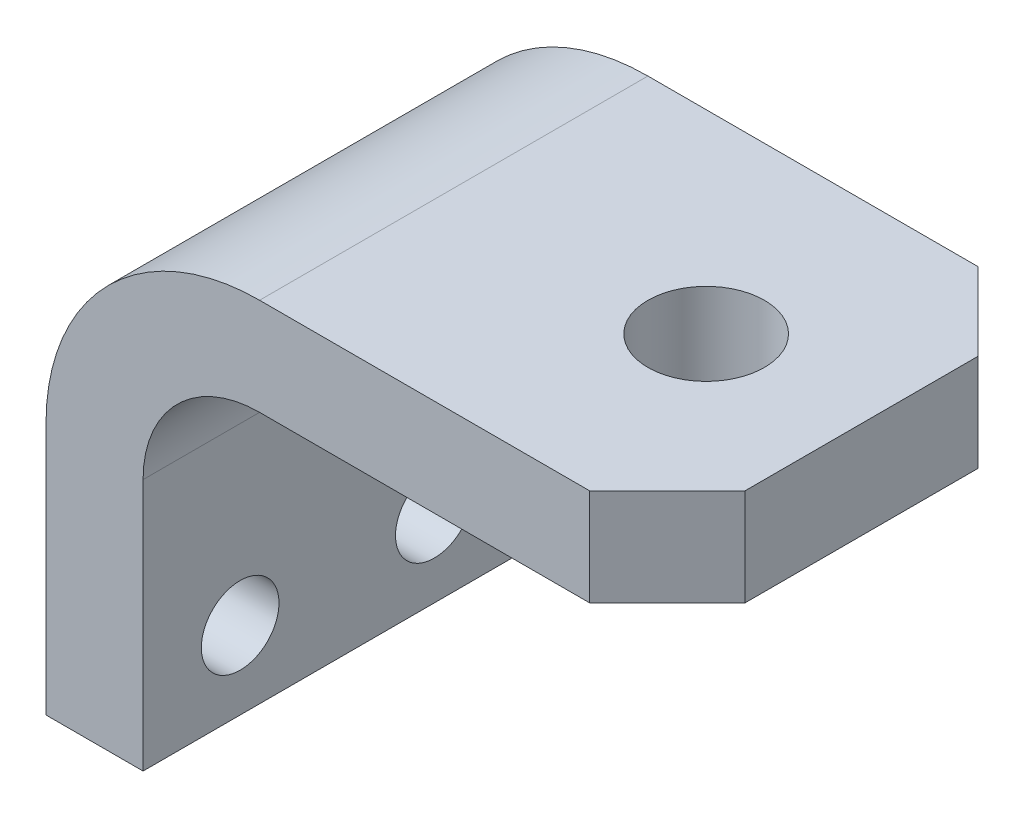
SolidWorks part; units mm, degrees
ref_plane "Front" through (0, 0, 0) normal (0, 0, 1) x (1, 0, 0)
ref_plane "Top" through (0, 0, 0) normal (0, 1, 0) x (1, 0, 0)
ref_plane "Right" through (0, 0, 0) normal (1, 0, 0) x (0, 0, -1)
sketch "Sketch1" plane through (0, 0, 0) normal (0, 0, 1) x (1, 0, 0)
  line L0 (-76.2, -60.325) -> (-76.2, -19.05)
  line L1 (25.4, 15.875) -> (-41.275, 15.875)
  line L2 (-76.2, -60.325) -> (-60.325, -60.325)
  line L3 (-60.325, -60.325) -> (-60.325, -19.05)
  line L4 (25.4, 0) -> (-41.275, 0)
  line L5 (25.4, 0) -> (25.4, 15.875)
  arc A0 (-41.275, 0) -> (-60.325, -19.05) centre (-41.275, -19.05) ccw
  arc A1 (-41.275, 15.875) -> (-76.2, -19.05) centre (-41.275, -19.05) ccw
  dimension "D3" = 19.05
  dimension "D4" = 15.875
  dimension "D1" = 101.6
  dimension "D2" = 76.2
  dimension "D5" = 25.4
extrude "Boss-Extrude1" add sketch "Sketch1" along normal mid plane 63.5
sketch "Sketch2" plane through (0, 15.875, 0) normal (0, 1, 0) x (1, 0, 0)
  circle A0 centre (0, 0) radius 9.525
  dimension "D1" = 19.05
extrude "Ball Anchor hole" cut sketch "Sketch2" against normal through all
sketch "Sketch3" plane through (0, 15.875, 0) normal (0, 1, 0) x (1, 0, 0)
  line L0 (12.7, 31.75) -> (25.4, 19.05)
  line L1 (25.4, 31.75) -> (-41.275, 31.75) construction
  line L2 (25.4, -31.75) -> (25.4, 31.75) construction
  line L3 (12.7, -31.75) -> (25.4, -19.05)
  line L4 (25.4, -31.75) -> (-41.275, -31.75) construction
  line L5 (12.7, 31.75) -> (25.4, 31.75)
  line L6 (25.4, 31.75) -> (25.4, 19.05)
  line L7 (25.4, -19.05) -> (25.4, -31.75)
  line L8 (25.4, -31.75) -> (12.7, -31.75)
  dimension "D1" = 12.7
  dimension "D2" = 12.7
  dimension "D3" = 45
  dimension "D4" = 45
extrude "45 Deg Corners" cut sketch "Sketch3" against normal through all
sketch "Sketch4" plane through (-60.325, 0, 0) normal (1, 0, 0) x (0, 0, -1)
  line L0 (-19.05, 15.875) -> (19.05, 15.875) construction
  line L1 (-31.75, -60.325) -> (-31.75, -19.05) construction
  circle A0 centre (-15.875, -47.625) radius 6.35
  circle A1 centre (15.875, -47.625) radius 6.35
  dimension "D1" = 12.7
  dimension "D2" = 63.5
  dimension "D3" = 63.5
  dimension "D4" = 15.875
  dimension "D5" = 31.75
extrude "Bolt Hole x 2" cut sketch "Sketch4" against normal up to next
